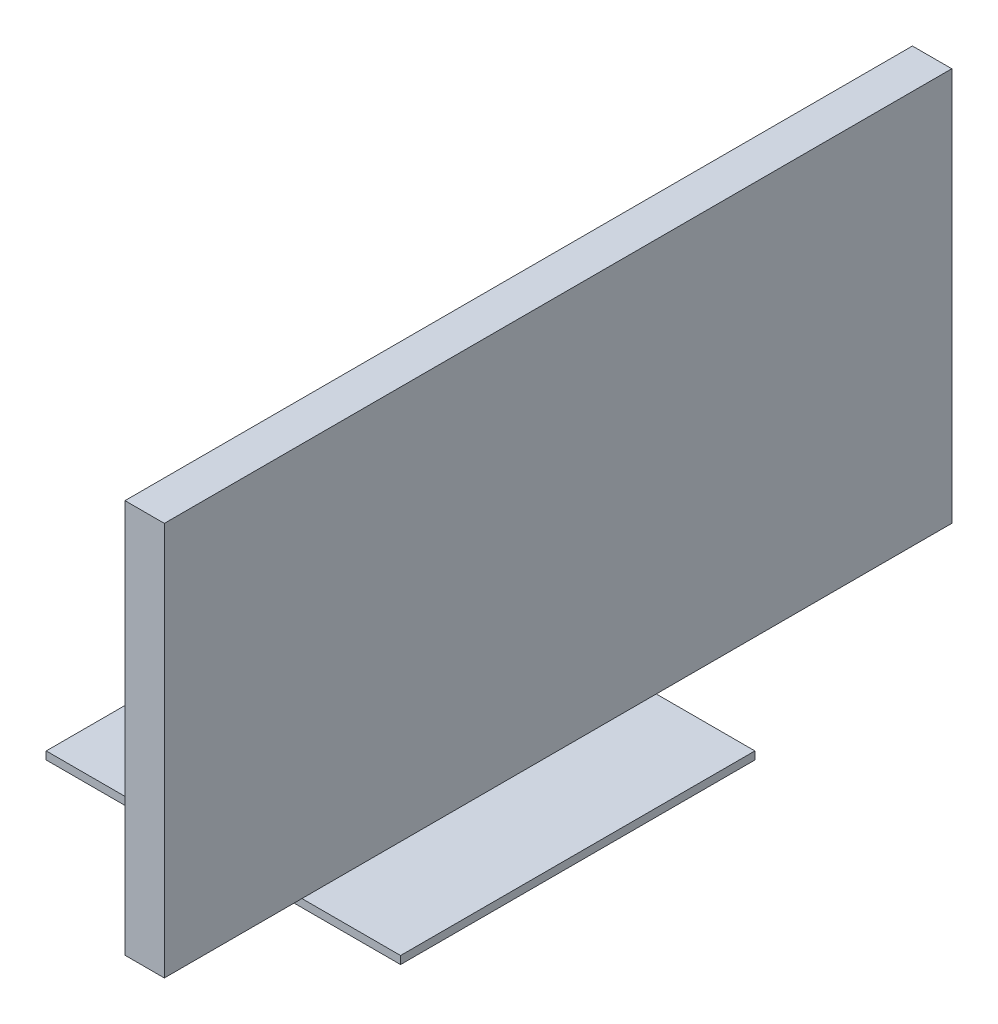
SolidWorks part; units mm, degrees
ref_plane "Front Plane" through (0, 0, 0) normal (0, 0, 1) x (1, 0, 0)
ref_plane "Top Plane" through (0, 0, 0) normal (0, 1, 0) x (1, 0, 0)
ref_plane "Right Plane" through (0, 0, 0) normal (1, 0, 0) x (0, 0, -1)
sketch "Sketch2" plane through (0, 0, 0) normal (0, 1, 0) x (1, 0, 0)
  line L1 (0, 0) -> (45, 0)
  line L2 (0, 0) -> (0, 45)
  line L3 (0, 45) -> (45, 45)
  line L4 (45, 0) -> (45, 45)
  dimension "D1" = 45
  dimension "D2" = 45
extrude "Boss-Extrude1" add sketch "Sketch2" along normal blind 1
sketch "Sketch4" plane through (0, 1, 0) normal (0, 1, 0) x (1, 0, 0)
  line L4 (17.5, 27.5) -> (27.5, 27.5)
  line L5 (17.5, 27.5) -> (17.5, 17.5)
  line L6 (17.5, 17.5) -> (27.5, 17.5)
  line L7 (27.5, 27.5) -> (27.5, 17.5)
  line L8 (17.5, 27.5) -> (27.5, 17.5) construction
  line L9 (17.5, 17.5) -> (27.5, 27.5) construction
  point P4 (22.5, 22.5)
  dimension "D1" = 10
  dimension "D2" = 10
extrude "Boss-Extrude3" add sketch "Sketch4" along normal blind 40 contours L4 L7 L6 L5
ref_plane "Plane1" through (17.5, 41, -17.5) normal (0, 0, 1) x (1, 0, 0)
sketch "Sketch10" plane through (17.5, 41, -17.5) normal (0, 0, 1) x (1, 0, 0)
  line L0 (0, 0) -> (10, -9.9496)
  line L1 (10, 0) -> (10, -40) construction
  line L2 (10, -9.9496) -> (17.9108, -1.9989)
  line L3 (17.9108, -1.9989) -> (8.3582, 7.5056)
  line L4 (8.3582, 7.5056) -> (0, 0)
extrude "Cut-Extrude4" cut sketch "Sketch10" against normal blind 30 contours L0 L2 L3 L4
sketch "Sketch16" plane through (17.5, 41, -17.5) normal (0, 0, 1) x (1, 0, 0)
  line L0 (10, -9.9496) -> (0, 0)
  line L1 (0, 0) -> (20, 0)
  line L2 (20, 0) -> (20, -9.9496)
  line L3 (20, -9.9496) -> (10, -9.9496)
  dimension "D1" = 10
extrude "Boss-Extrude8" add sketch "Sketch16" against normal blind 10 contours L3 L0 L1 L2
sketch "Sketch18" plane through (37.5, 0, 0) normal (1, 0, 0) x (0, 0, -1)
  line L1 (27.5, 31.0504) -> (27.5, 41)
  line L4 (-27.5, 11.0252) -> (72.5, 11.0252)
  line L5 (-27.5, 11.0252) -> (-27.5, 61.0252)
  line L6 (-27.5, 61.0252) -> (72.5, 61.0252)
  line L7 (72.5, 11.0252) -> (72.5, 61.0252)
  line L8 (-27.5, 11.0252) -> (72.5, 61.0252) construction
  line L9 (-27.5, 61.0252) -> (72.5, 11.0252) construction
  point P4 (22.5, 36.0252)
  dimension "D1" = 50
  dimension "D2" = 100
extrude "Boss-Extrude9" add sketch "Sketch18" along normal blind 5 contours L5 L6 L7 L4
